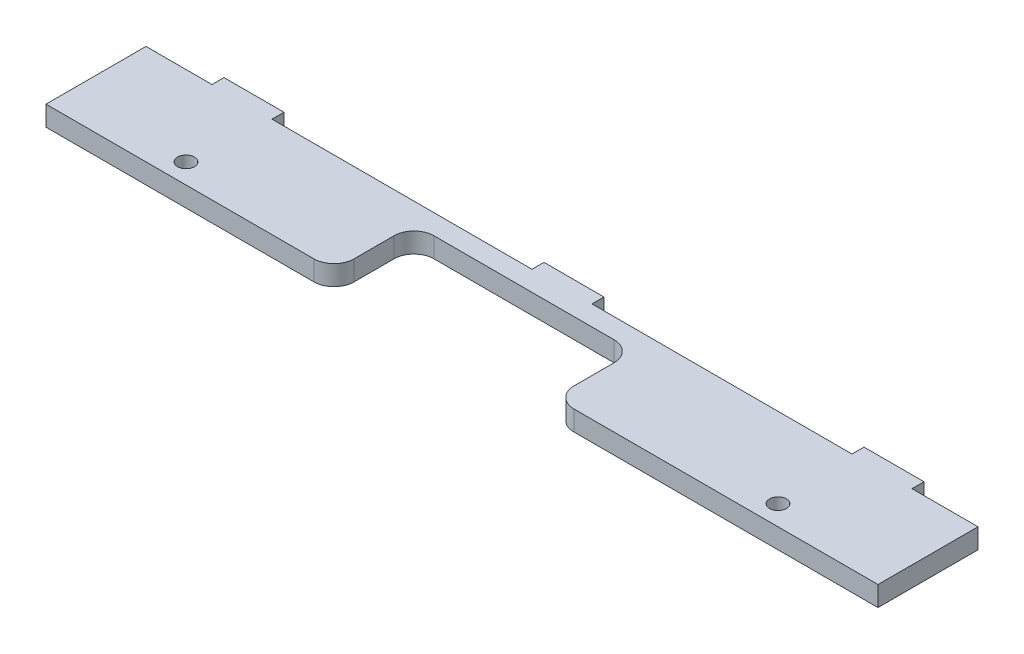
SolidWorks part; units mm, degrees
ref_plane "Front Plane" through (0, 0, 0) normal (0, 0, 1) x (1, 0, 0)
ref_plane "Top Plane" through (0, 0, 0) normal (0, 1, 0) x (1, 0, 0)
ref_plane "Right Plane" through (0, 0, 0) normal (1, 0, 0) x (0, 0, -1)
sketch "Sketch1" plane through (0, 0, 0) normal (0, 1, 0) x (1, 0, 0)
  line L0 (-59.7453, 16.668) -> (148.2547, 16.668)
  line L2 (-59.7453, 16.668) -> (-59.7453, -8.332)
  line L3 (-59.7453, -8.332) -> (148.2547, -8.332)
  line L4 (148.2547, 16.668) -> (148.2547, -8.332)
  dimension "D1" = 208
  dimension "D6" = 25
extrude "Boss-Extrude1" add sketch "Sketch1" along normal blind 5
sketch "Sketch6" plane through (0, 0, 0) normal (0, -1, 0) x (-1, 0, 0)
  line L0 (-72.2547, -8.332) -> (-7.2547, -8.332)
  line L2 (-67.2547, -3.332) -> (-67.2547, 6.668)
  line L3 (-62.2547, 11.668) -> (-17.2547, 11.668)
  line L4 (-12.2547, -3.332) -> (-12.2547, 6.668)
  line L6 (59.7453, 16.668) -> (59.7453, -8.332) construction
  arc A0 (-67.2547, 6.668) -> (-62.2547, 11.668) centre (-62.2547, 6.668) cw
  arc A1 (-17.2547, 11.668) -> (-12.2547, 6.668) centre (-17.2547, 6.668) cw
  arc A2 (-72.2547, -8.332) -> (-67.2547, -3.332) centre (-72.2547, -3.332) ccw
  arc A3 (-12.2547, -3.332) -> (-7.2547, -8.332) centre (-7.2547, -3.332) ccw
  point P10 (-67.2547, 11.668)
  point P13 (-12.2547, 11.668)
  point P18 (-67.2547, -8.332)
  dimension "D5" = 5
  dimension "D1" = 5
  dimension "D2" = 72
  dimension "D3" = 55
  dimension "D4" = 20
extrude "Surucu Boslugu" cut sketch "Sketch6" against normal through all
sketch "Sketch7" plane through (0, 0, 0) normal (0, -1, 0) x (1, 0, 0)
  line L0 (-59.7453, -16.668) -> (-59.7453, 8.332) construction
  line L1 (-59.7453, 8.332) -> (7.2547, 8.332) construction
  circle A0 centre (-29.7453, 3.332) radius 2.1
  circle A1 centre (118.2547, 3.332) radius 2.1
  dimension "D1" = 4.2
  dimension "D4" = 4.2
  dimension "D2" = 30
  dimension "D3" = 5
  dimension "D5" = 148
extrude "Kasa Baglanti" cut sketch "Sketch7" against normal through all
sketch "Sketch8" plane through (0, 0, 0) normal (0, -1, 0) x (1, 0, 0)
  line L0 (-59.7453, -16.668) -> (148.2547, -16.668) construction
  line L1 (44.2547, -16.668) -> (44.2547, -18.168) construction
  line L2 (116.7547, -16.668) -> (131.7547, -16.668)
  line L3 (36.7547, -16.668) -> (51.7547, -16.668)
  line L4 (36.7547, -16.668) -> (36.7547, -19.668)
  line L5 (36.7547, -19.668) -> (51.7547, -19.668)
  line L6 (51.7547, -16.668) -> (51.7547, -19.668)
  line L7 (44.2547, -19.668) -> (44.2547, -16.668) construction
  line L8 (36.7547, -18.168) -> (51.7547, -18.168) construction
  line L9 (116.7547, -16.668) -> (116.7547, -19.668)
  line L10 (116.7547, -19.668) -> (131.7547, -19.668)
  line L11 (131.7547, -16.668) -> (131.7547, -19.668)
  line L12 (124.2547, -16.668) -> (124.2547, -18.168) construction
  line L13 (124.2547, -19.668) -> (124.2547, -16.668) construction
  line L14 (116.7547, -18.168) -> (131.7547, -18.168) construction
  line L15 (-43.2453, -16.668) -> (-28.2453, -16.668)
  line L16 (-43.2453, -16.668) -> (-43.2453, -19.668)
  line L17 (-43.2453, -19.668) -> (-28.2453, -19.668)
  line L18 (-28.2453, -16.668) -> (-28.2453, -19.668)
  line L19 (-35.7453, -16.668) -> (-35.7453, -18.168) construction
  line L20 (-35.7453, -19.668) -> (-35.7453, -16.668) construction
  line L21 (-43.2453, -18.168) -> (-28.2453, -18.168) construction
  dimension "D1" = 0
  dimension "D2" = 3
  dimension "D3" = 15
  dimension "D4" = 2
  dimension "D5" = 2
extrude "Yan Baglanti" add sketch "Sketch8" against normal through all
